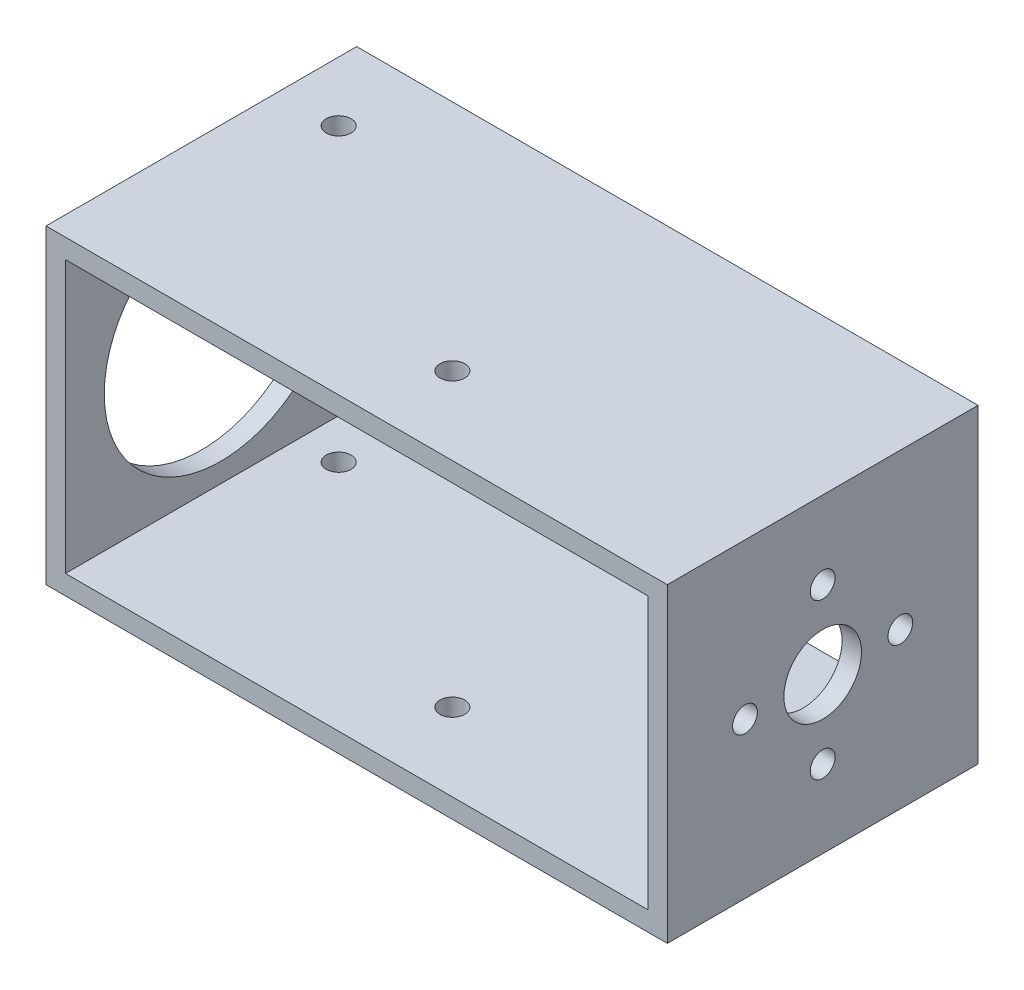
SolidWorks part; units mm, degrees
ref_plane "正面" through (0, 0, 0) normal (0, 0, 1) x (1, 0, 0)
ref_plane "平面" through (0, 0, 0) normal (0, 1, 0) x (1, 0, 0)
ref_plane "右側面" through (0, 0, 0) normal (1, 0, 0) x (0, 0, -1)
sketch "ｽｹｯﾁ1" plane through (0, 0, 0) normal (0, 0, 1) x (1, 0, 0)
  line L1 (-40, -20) -> (40, -20)
  line L2 (-40, -20) -> (-40, 20)
  line L3 (-40, 20) -> (40, 20)
  line L4 (40, -20) -> (40, 20)
  line L5 (-40, -20) -> (40, 20) construction
  line L6 (-40, 20) -> (40, -20) construction
  line L7 (-37.5, -17.5) -> (37.5, -17.5)
  line L8 (-37.5, -17.5) -> (-37.5, 17.5)
  line L9 (-37.5, 17.5) -> (37.5, 17.5)
  line L10 (37.5, -17.5) -> (37.5, 17.5)
  line L11 (-37.5, -17.5) -> (37.5, 17.5) construction
  line L12 (-37.5, 17.5) -> (37.5, -17.5) construction
  point P0 (0, 0)
  point P6 (0, 0)
  dimension "D1" = 40
  dimension "D2" = 80
  dimension "D3" = 2.5
  dimension "D4" = 2.5
extrude "ﾎﾞｽ - 押し出し1" add sketch "ｽｹｯﾁ1" along normal mid plane 40
sketch "ｽｹｯﾁ3" plane through (40, 0, 0) normal (1, 0, 0) x (0, 0, -1)
  circle A0 centre (0, 0) radius 10 construction
  circle A1 centre (0, 10) radius 1.6
  circle A2 centre (10, 0) radius 1.6
  circle A3 centre (0, -10) radius 1.6
  circle A4 centre (-10, 0) radius 1.6
  circle A5 centre (0, 0) radius 5
  dimension "D1" = 3.2
  dimension "D2" = 20
  dimension "D3" = 10
extrude "ｶｯﾄ - 押し出し1" cut sketch "ｽｹｯﾁ3" against normal up to next
sketch "ｽｹｯﾁ4" plane through (-40, 0, 0) normal (-1, 0, 0) x (0, 0, 1)
  circle A0 centre (0, 0) radius 15
  dimension "D1" = 30
extrude "ｶｯﾄ - 押し出し2" cut sketch "ｽｹｯﾁ4" against normal up to next
sketch "ｽｹｯﾁ5" plane through (0, -20, 0) normal (0, -1, 0) x (1, 0, 0)
  line L0 (-32.3205, -10) -> (2.3205, 10) construction
  line L1 (-15, 0) -> (-40, 0) construction
  line L2 (-40, 20) -> (-40, -20) construction
  circle A0 centre (-32.3205, -10) radius 1.6
  circle A1 centre (2.3205, 10) radius 1.6
  dimension "D4" = 3.2
  dimension "D1" = 25
  dimension "D2" = 30
  dimension "D3" = 40
extrude "ｶｯﾄ - 押し出し3" cut sketch "ｽｹｯﾁ5" against normal through all
